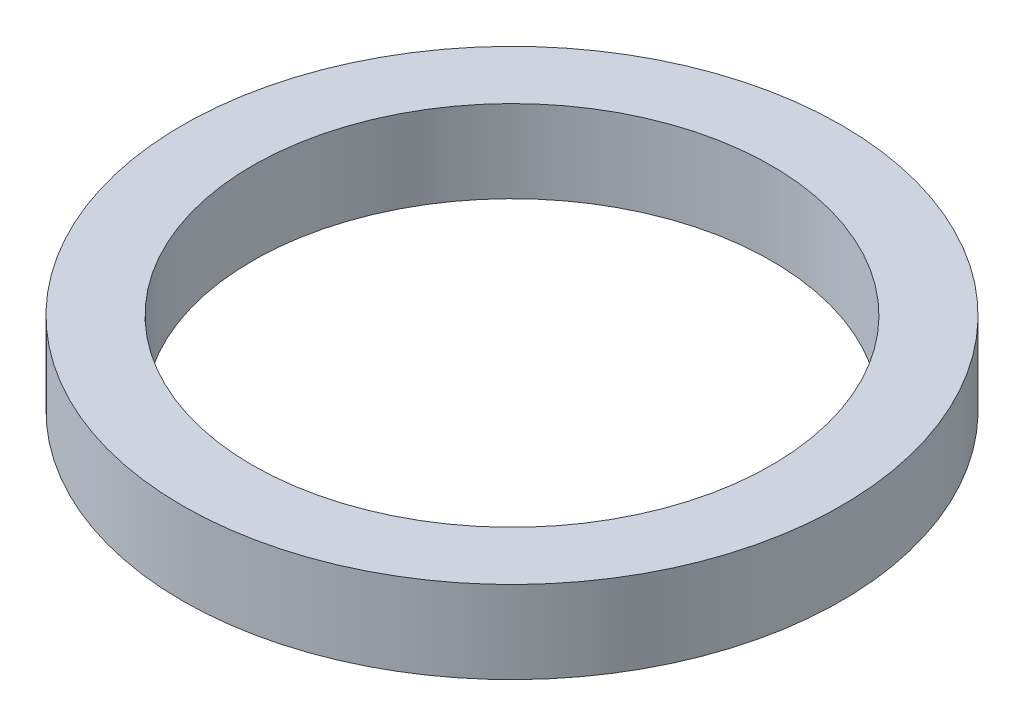
SolidWorks part; units mm, degrees
material "C (Graphite)"
ref_plane "Front Plane" through (0, 0, 0) normal (0, 0, 1) x (1, 0, 0)
ref_plane "Top Plane" through (0, 0, 0) normal (0, 1, 0) x (1, 0, 0)
ref_plane "Right Plane" through (0, 0, 0) normal (1, 0, 0) x (0, 0, -1)
sketch "Sketch1" plane through (0, 0, 0) normal (0, 1, 0) x (1, 0, 0)
  circle A0 centre (0, 0) radius 5
  circle A1 centre (0, 0) radius 6.35
  dimension "D1" = 10
  dimension "D2" = 12.7
extrude "Boss-Extrude1" add sketch "Sketch1" along normal blind 1.5875
